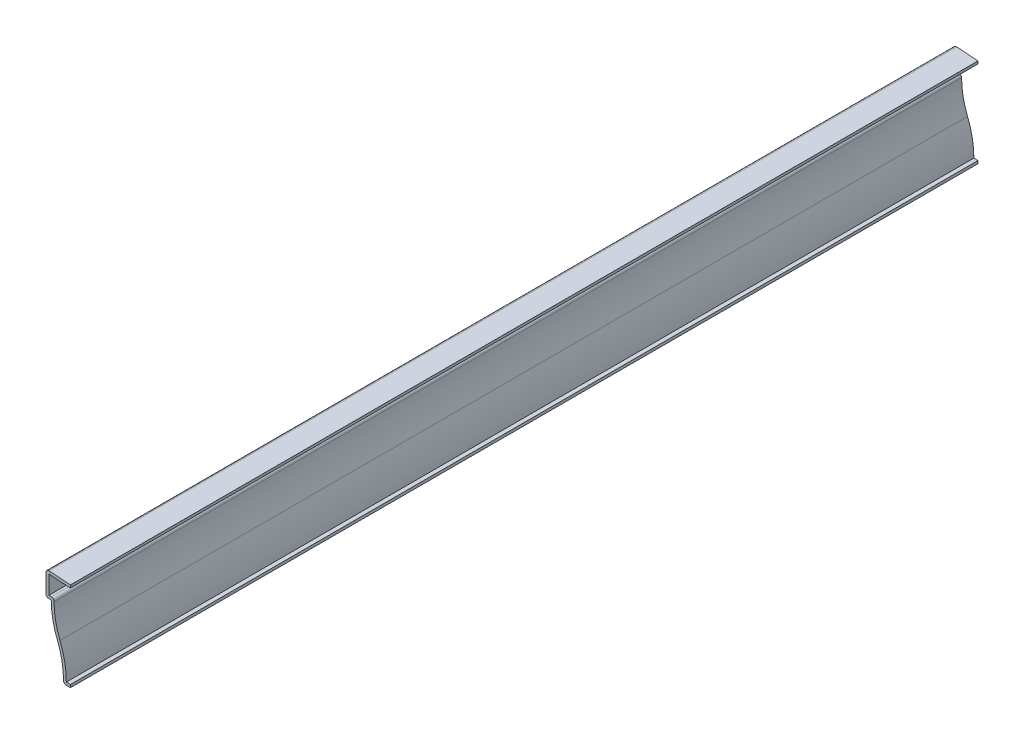
SolidWorks part; units mm, degrees
ref_plane "Front Plane" through (0, 0, 0) normal (0, 0, 1) x (1, 0, 0)
ref_plane "Top Plane" through (0, 0, 0) normal (0, 1, 0) x (1, 0, 0)
ref_plane "Right Plane" through (0, 0, 0) normal (1, 0, 0) x (0, 0, -1)
sketch "Sketch1" plane through (0, 0, 0) normal (0, 0, 1) x (1, 0, 0)
  line L0 (0, 0) -> (-3.175, 0)
  line L1 (-8.7312, 30.1625) -> (-11.1125, 30.1625)
  line L2 (-11.1125, 30.1625) -> (-11.1125, 41.275)
  line L3 (-11.1125, 41.275) -> (0, 40.4812)
  line L4 (0, 0) -> (0, 47.8693) construction
  arc A0 (-3.175, 0) -> (-5.9407, 15.7727) centre (-41.647, 1.3828) ccw
  arc A1 (-5.9407, 15.7727) -> (-8.7312, 30.1625) centre (29.7656, 30.1625) cw
  point P9 (0, 0)
  point P12 (-7.9815, 18.1231)
  point P13 (-9.4939, 30.1625)
  point P14 (-10.0217, 30.1625)
  dimension "D2" = 38.4969
  dimension "D3" = 2.3813
  dimension "D4" = 5.5811
  dimension "D1" = 3.175
  dimension "D5" = 30.1625
  dimension "D6" = 11.1125
  dimension "D8" = 0.7937
  dimension "D9" = 11.1125
extrude "Extrude-Thin1" add sketch "Sketch1" against normal blind 412.75 thin
fillet "Fillet1" radius 1.27 4 edges at (-11.1125, 30.1625, -206.375) (-11.1125, 41.275, -206.375) (-3.175, 0, -206.375) (-7.4396, 31.4325, -206.375)
